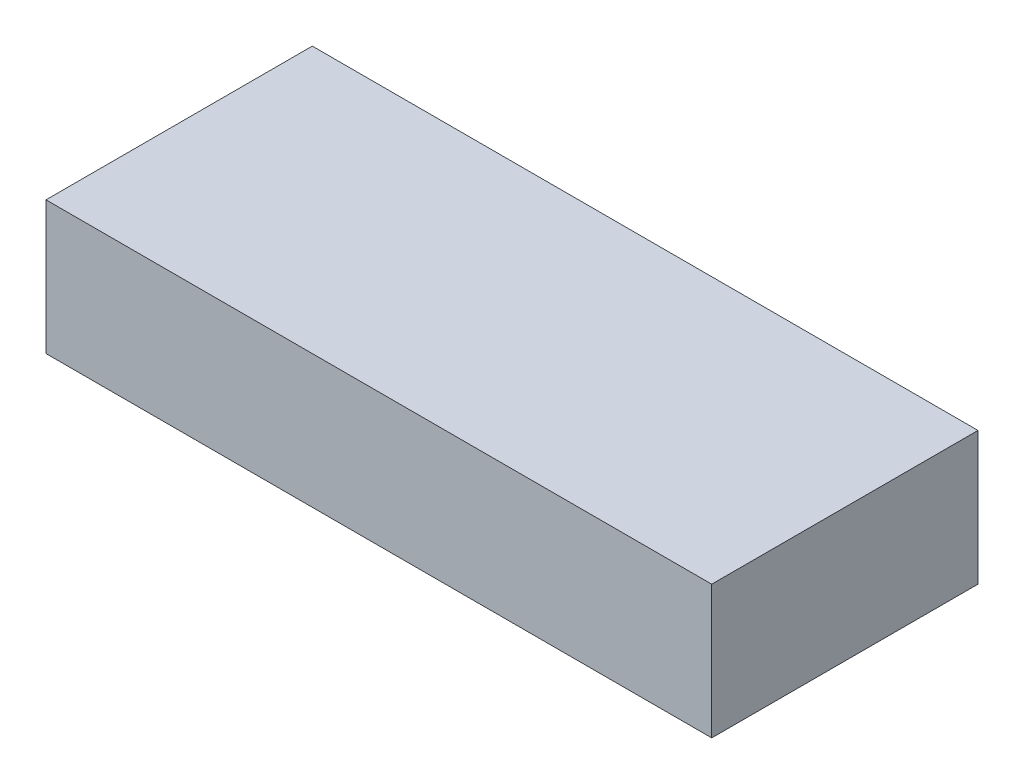
SolidWorks part; units mm, degrees
material "Maple"
ref_plane "Front Plane" through (0, 0, 0) normal (0, 0, 1) x (1, 0, 0)
ref_plane "Top Plane" through (0, 0, 0) normal (0, 1, 0) x (1, 0, 0)
ref_plane "Right Plane" through (0, 0, 0) normal (1, 0, 0) x (0, 0, -1)
sketch "Sketch1" plane through (0, 0, 0) normal (0, 1, 0) x (1, 0, 0)
  line L1 (-15, 6) -> (15, 6)
  line L2 (-15, 6) -> (-15, -6)
  line L3 (-15, -6) -> (15, -6)
  line L4 (15, 6) -> (15, -6)
  line L5 (-15, 6) -> (15, -6) construction
  line L6 (-15, -6) -> (15, 6) construction
  point P0 (0, 0)
  dimension "D1" = 30
  dimension "D2" = 12
extrude "Boss-Extrude1" add sketch "Sketch1" along normal blind 6
ref_plane "Plane1" through (0, 3, 0) normal (0, 1, 0) x (1, 0, 0)
